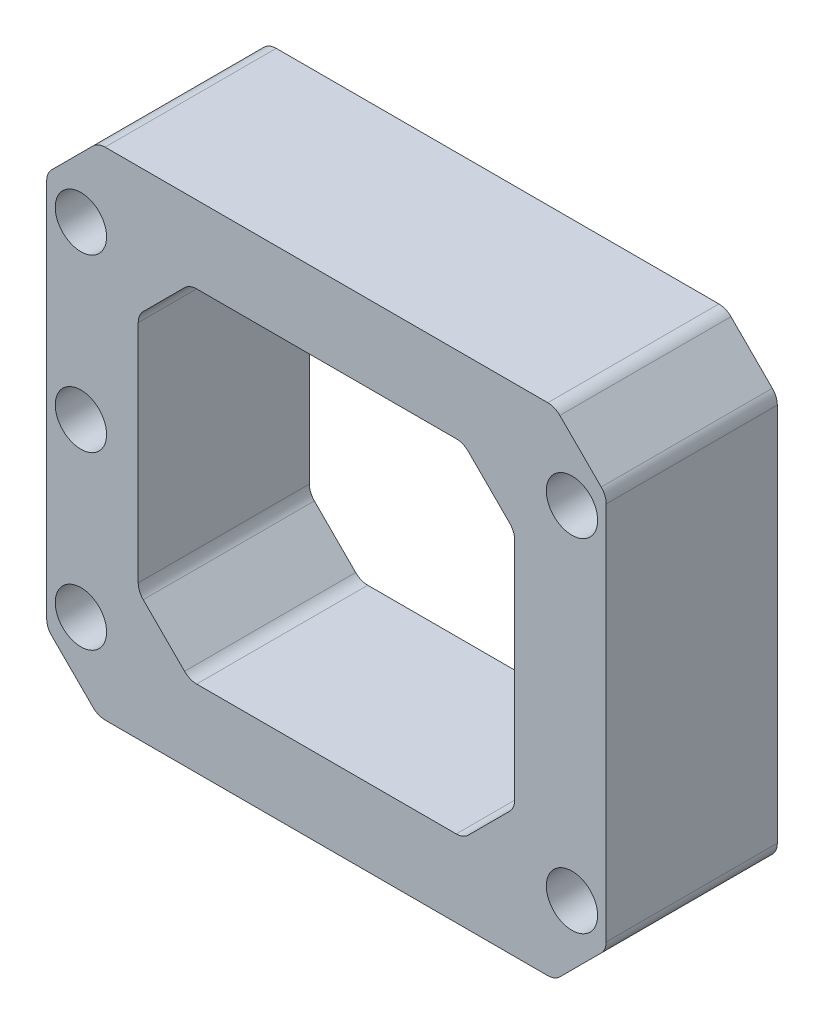
SolidWorks part; units mm, degrees
material "Thornel Mat VMA"
ref_plane "前视基准面" through (0, 0, 0) normal (0, 0, 1) x (1, 0, 0)
ref_plane "上视基准面" through (0, 0, 0) normal (0, 1, 0) x (1, 0, 0)
ref_plane "右视基准面" through (0, 0, 0) normal (1, 0, 0) x (0, 0, -1)
sketch "草图1" plane through (0, 0, 0) normal (0, 0, 1) x (1, 0, 0)
  line L1 (-16.35, 14.5) -> (16.35, 14.5)
  line L2 (-16.35, 14.5) -> (-16.35, -14.5)
  line L3 (-16.35, -14.5) -> (16.35, -14.5)
  line L4 (16.35, 14.5) -> (16.35, -14.5)
  line L5 (-16.35, 14.5) -> (16.35, -14.5) construction
  line L6 (-16.35, -14.5) -> (16.35, 14.5) construction
  line L7 (-14.35, 10) -> (14.35, 10) construction
  line L8 (-14.35, 10) -> (-14.35, -10) construction
  line L9 (-14.35, -10) -> (14.35, -10) construction
  line L10 (14.35, 10) -> (14.35, -10) construction
  line L11 (-14.35, 10) -> (14.35, -10) construction
  line L12 (-14.35, -10) -> (14.35, 10) construction
  circle A0 centre (-14.35, -10) radius 1.5
  circle A1 centre (-14.35, 10) radius 1.5
  circle A2 centre (14.35, 10) radius 1.5
  circle A3 centre (14.35, -10) radius 1.5
  circle A4 centre (-14.35, 0) radius 1.5
  point P0 (0, 0)
  point P6 (0, 0)
  dimension "D5" = 3
  dimension "D1" = 29
  dimension "D2" = 28.7
  dimension "D3" = 32.7
  dimension "D4" = 20
extrude "凸台-拉伸1" add sketch "草图1" along normal blind 10
chamfer "倒角1" distance 3 angle 45 4 edges at (16.35, -14.5, 5) (16.35, 14.5, 5) (-16.35, -14.5, 5) (-16.35, 14.5, 5)
sketch "草图2" plane through (0, 0, 10) normal (0, 0, 1) x (1, 0, 0)
  line L0 (-11, 7) -> (-8, 10)
  line L1 (-8, 10) -> (8, 10)
  line L2 (-11, 7) -> (-11, -7)
  line L3 (-8, -10) -> (8, -10)
  line L4 (11, 7) -> (11, -7)
  line L5 (-11, 10) -> (11, -10) construction
  line L6 (-11, -10) -> (11, 10) construction
  line L7 (8, 10) -> (11, 7)
  line L8 (-11, -7) -> (-8, -10)
  line L9 (8, -10) -> (11, -7)
  point P0 (0, 0)
  dimension "D1" = 22
  dimension "D2" = 20
extrude "切除-拉伸1" cut sketch "草图2" against normal through all
fillet "圆角1" radius 1 16 edges at (16.35, 11.5, 5) (13.35, 14.5, 5) (-13.35, 14.5, 5) (-16.35, 11.5, 5) (-16.35, -11.5, 5) (-13.35, -14.5, 5) (13.35, -14.5, 5) (16.35, -11.5, 5) (11, 7, 5) (11, -7, 5) (8, -10, 5) (-8, -10, 5) (-11, -7, 5) (-8, 10, 5) (8, 10, 5) (-11, 7, 5)
